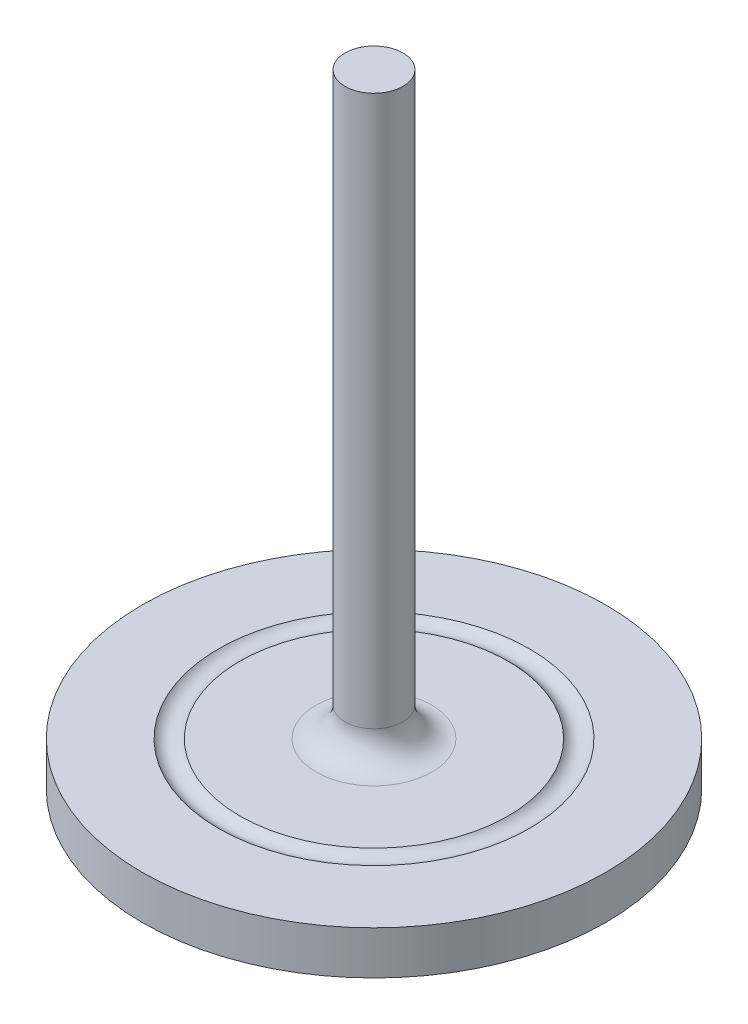
SolidWorks part; units mm, degrees
ref_plane "Front Plane" through (0, 0, 0) normal (0, 0, 1) x (1, 0, 0)
ref_plane "Top Plane" through (0, 0, 0) normal (0, 1, 0) x (1, 0, 0)
ref_plane "Right Plane" through (0, 0, 0) normal (1, 0, 0) x (0, 0, -1)
sketch "Sketch1" plane through (0, 0, 0) normal (0, 1, 0) x (1, 0, 0)
  circle A0 centre (0, 0) radius 80
  dimension "D1" = 160
extrude "Boss-Extrude1" add sketch "Sketch1" along normal blind 15
ref_plane "Plane2" through (0, 18, 0) normal (0, 1, 0) x (1, 0, 0)
sketch "Sketch29" plane through (0, 18, 0) normal (0, 1, 0) x (1, 0, 0)
  circle A0 centre (0, 0) radius 50
  dimension "D1" = 100
sketch "Sketch16" plane through (0, 15, 0) normal (0, 1, 0) x (1, 0, 0)
  circle A0 centre (0, 0) radius 10
  dimension "D1" = 20
extrude "Boss-Extrude2" add sketch "Sketch16" along normal blind 200
fillet "Fillet1" radius 10 1 edges at (0, 15, 10)
sweep "Cut-Sweep2" cut path "Sketch29" circular profile diameter 9.525 parameters "D3"=9.525
